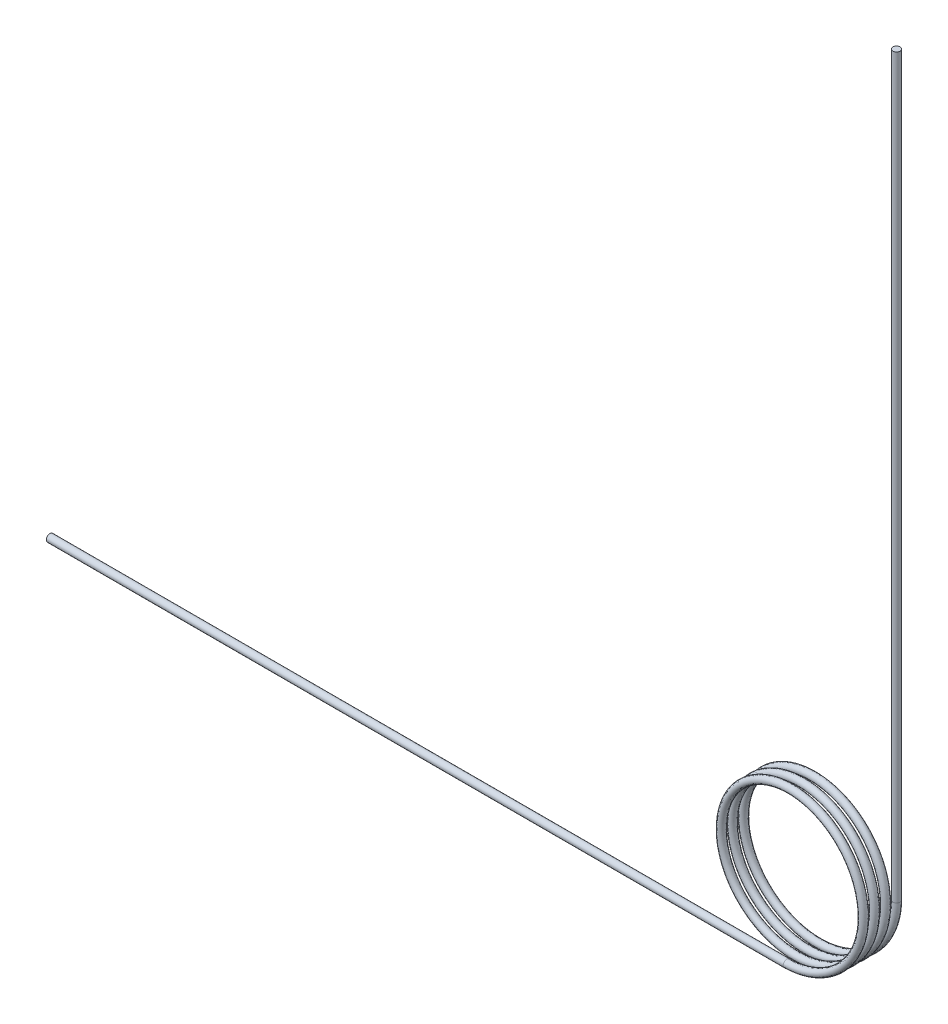
SolidWorks part; units mm, degrees
ref_plane "前视基准面" through (0, 0, 0) normal (0, 0, 1) x (1, 0, 0)
ref_plane "上视基准面" through (0, 0, 0) normal (0, 1, 0) x (1, 0, 0)
ref_plane "右视基准面" through (0, 0, 0) normal (1, 0, 0) x (0, 0, -1)
sketch "草图1" plane through (0, 0, 0) normal (0, 0, 1) x (1, 0, 0)
  circle A0 centre (0, 0) radius 2
  dimension "D1" = 4
curve "螺旋线/涡状线1" pitch 0.3 height 0.975 turns 3.25
ref_plane "基准面2" through (0, 0, 0) normal (0, 1, 0) x (1, 0, 0)
sketch "草图3" plane through (0, 0, 0) normal (0, 1, 0) x (1, 0, 0)
  circle A0 centre (2, 0) radius 0.1
  spline S0 degree 3 poles (2, 0) (2, -0.0063) (1.8917, -0.0191) (1.43, -0.0382) (0.742, -0.0574) (-0.0633, -0.0765) (-0.8586, -0.0956) (-1.518, -0.1147) (-1.9374, -0.1338) (-2.0503, -0.1529) (-1.8388, -0.1721) (-1.3365, -0.1912) (-0.6227, -0.2103) (0.1895, -0.2294) (0.9718, -0.2485) (1.6004, -0.2676) (1.9757, -0.2868) (2.0386, -0.3059) (1.779, -0.325) (1.2379, -0.3441) (0.501, -0.3632) (-0.3151, -0.3824) (-1.0814, -0.4015) (-1.6766, -0.4206) (-2.0066, -0.4397) (-2.0192, -0.4588) (-1.7124, -0.4779) (-1.1346, -0.4971) (-0.3775, -0.5162) (0.4395, -0.5353) (1.1868, -0.5544) (1.7465, -0.5735) (2.0298, -0.5926) (1.9921, -0.6118) (1.6393, -0.6309) (1.0271, -0.65) (0.2524, -0.6691) (-0.5621, -0.6882) (-1.2878, -0.7074) (-1.8097, -0.7265) (-2.0454, -0.7456) (-1.9575, -0.7647) (-1.5599, -0.7838) (-0.9156, -0.8029) (-0.1265, -0.8221) (0.6827, -0.8412) (1.3839, -0.8603) (1.8661, -0.8794) (2.0532, -0.8985) (1.9155, -0.9176) (1.4745, -0.9368) (0.8015, -0.9559) (0.2652, -0.9687) (0, -0.975) knots 0 0 0 0 0.019608 0.039216 0.058824 0.078431 0.098039 0.117647 0.137255 0.156863 0.176471 0.196078 0.215686 0.235294 0.254902 0.27451 0.294118 0.313725 0.333333 0.352941 0.372549 0.392157 0.411765 0.431373 0.45098 0.470588 0.490196 0.509804 0.529412 0.54902 0.568627 0.588235 0.607843 0.627451 0.647059 0.666667 0.686275 0.705882 0.72549 0.745098 0.764706 0.784314 0.803922 0.823529 0.843137 0.862745 0.882353 0.901961 0.921569 0.941176 0.960784 0.980392 1 1 1 1 construction
  dimension "D1" = 0.2
sweep "扫描1" add profiles "草图3" path "螺旋线/涡状线1"
sketch "草图5" plane through (0, 0, 0) normal (0, 1, 0) x (1, 0, 0)
  circle A0 centre (2, 0) radius 0.1
extrude "凸台-拉伸2" add sketch "草图5" along normal blind 20
sketch "草图6" plane through (0, 0, 0) normal (-1, 0, 0) x (0, 0, 1)
  circle A0 centre (0.975, -2) radius 0.1
extrude "凸台-拉伸3" add sketch "草图6" along normal blind 20
